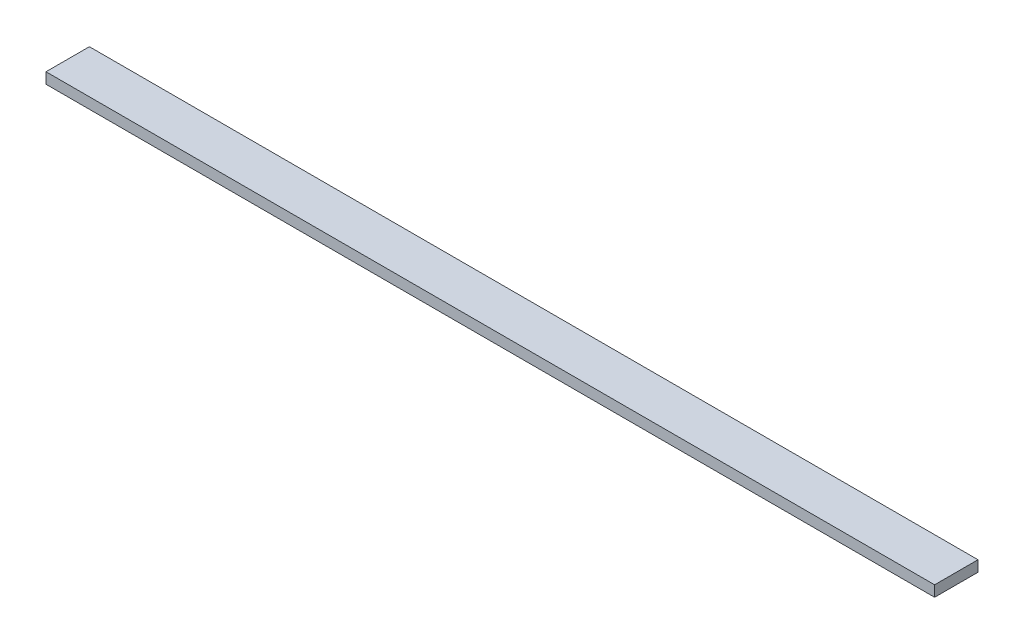
SolidWorks part; units mm, degrees
ref_plane "Front Plane" through (0, 0, 0) normal (0, 0, 1) x (1, 0, 0)
ref_plane "Top Plane" through (0, 0, 0) normal (0, 1, 0) x (1, 0, 0)
ref_plane "Right Plane" through (0, 0, 0) normal (1, 0, 0) x (0, 0, -1)
sketch "Sketch1" plane through (0, 0, 0) normal (0, 1, 0) x (1, 0, 0)
  line L1 (0, 0) -> (260.096, 0)
  line L2 (0, 0) -> (0, 12.7)
  line L3 (0, 12.7) -> (260.096, 12.7)
  line L4 (260.096, 0) -> (260.096, 12.7)
  dimension "D1" = 12.7
  dimension "D2" = 260.096
extrude "Boss-Extrude1" add sketch "Sketch1" along normal blind 3.175
